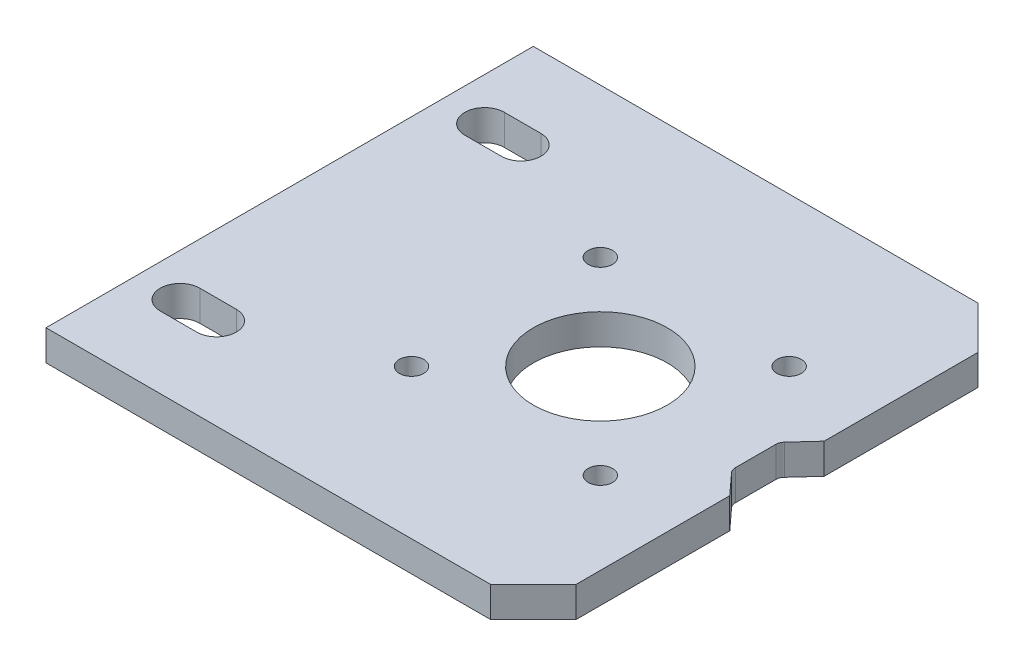
SolidWorks part; units mm, degrees
material "6063-T5"
ref_plane "Piano frontale" through (0, 0, 0) normal (0, 0, 1) x (1, 0, 0)
ref_plane "Piano superiore" through (0, 0, 0) normal (0, 1, 0) x (1, 0, 0)
ref_plane "Piano destro" through (0, 0, 0) normal (1, 0, 0) x (0, 0, -1)
sketch "Schizzo1" plane through (0, 0, 0) normal (0, 0, 1) x (1, 0, 0)
  line L1 (0, 0) -> (80, 0)
  line L2 (0, 0) -> (0, 5)
  line L3 (0, 5) -> (80, 5)
  line L4 (80, 0) -> (80, 5)
  dimension "D1" = 5
  dimension "D2" = 80
extrude "Estrusione-Estrusione1" add sketch "Schizzo1" along normal blind 80
sketch "Schizzo4" plane through (0, 5, 0) normal (0, 1, 0) x (1, 0, 0)
  line L0 (0, -80) -> (0, 0) construction
  line L3 (19.8289, -40) -> (54.8798, -40) construction
  line L4 (80, -80) -> (0, -80) construction
  line L5 (80, 0) -> (0, 0) construction
  circle A0 centre (51, -40) radius 11
  dimension "D1" = 22
  dimension "D2" = 51
extrude "Taglio-Estrusione1" cut sketch "Schizzo4" against normal through all
sketch "Schizzo6" plane through (0, 5, 0) normal (0, 1, 0) x (1, 0, 0)
  line L0 (42.0101, -40) -> (55.783, -40) construction
  line L1 (51, -40) -> (51, -30.1482) construction
  line L2 (80, -80) -> (0, -80) construction
  line L3 (80, 0) -> (0, 0) construction
  circle A0 centre (35.5, -24.5) radius 2
  circle A1 centre (66.5, -24.5) radius 2
  circle A2 centre (66.5, -55.5) radius 2
  circle A3 centre (35.5, -55.5) radius 2
  dimension "D1" = 4
  dimension "D2" = 31
  dimension "D3" = 31
  dimension "D4" = 15.5
extrude "Taglio-Estrusione3" cut sketch "Schizzo6" against normal through all
chamfer "Chamfer1" distance 7 angle 45 2 edges at (80, 2.5, 0) (80, 2.5, 80)
sketch "Sketch1" plane through (0, 5, 0) normal (0, 1, 0) x (1, 0, 0)
  line L0 (7, -15) -> (13, -15) construction
  line L1 (7, -11.75) -> (13, -11.75)
  line L2 (7, -18.25) -> (13, -18.25)
  line L3 (0, -40) -> (80, -40) construction
  line L4 (0, -80) -> (0, 0) construction
  line L5 (80, -73) -> (80, -7) construction
  line L6 (7, -65) -> (13, -65) construction
  line L7 (7, -68.25) -> (13, -68.25)
  line L8 (7, -61.75) -> (13, -61.75)
  arc A0 (7, -11.75) -> (7, -18.25) centre (7, -15) ccw
  arc A1 (13, -18.25) -> (13, -11.75) centre (13, -15) ccw
  arc A2 (7, -68.25) -> (7, -61.75) centre (7, -65) cw
  arc A3 (13, -61.75) -> (13, -68.25) centre (13, -65) cw
  point P3 (10, -15)
  point P16 (10, -65)
  dimension "D1" = 6.5
  dimension "D2" = 6
  dimension "D3" = 10
extrude "Cut-Extrude1" cut sketch "Sketch1" against normal through all
sketch "Sketch2" plane through (0, 5, 0) normal (0, 1, 0) x (1, 0, 0)
  line L0 (80, -32.246) -> (76.4803, -36.097)
  line L1 (80, -73) -> (80, -7) construction
  line L2 (76.4803, -36.097) -> (76.4803, -43.903)
  line L3 (76.4803, -40) -> (80, -40) construction
  line L4 (80, -47.754) -> (76.4803, -43.903)
  line L5 (80, -32.246) -> (80, -47.754)
extrude "Cut-Extrude2" cut sketch "Sketch2" against normal through all
fillet "Fillet1" radius 1.5 1 edges at (76.4803, 2.5, 36.097)
fillet "Fillet2" radius 1.5 1 edges at (76.4803, 2.5, 43.903)
